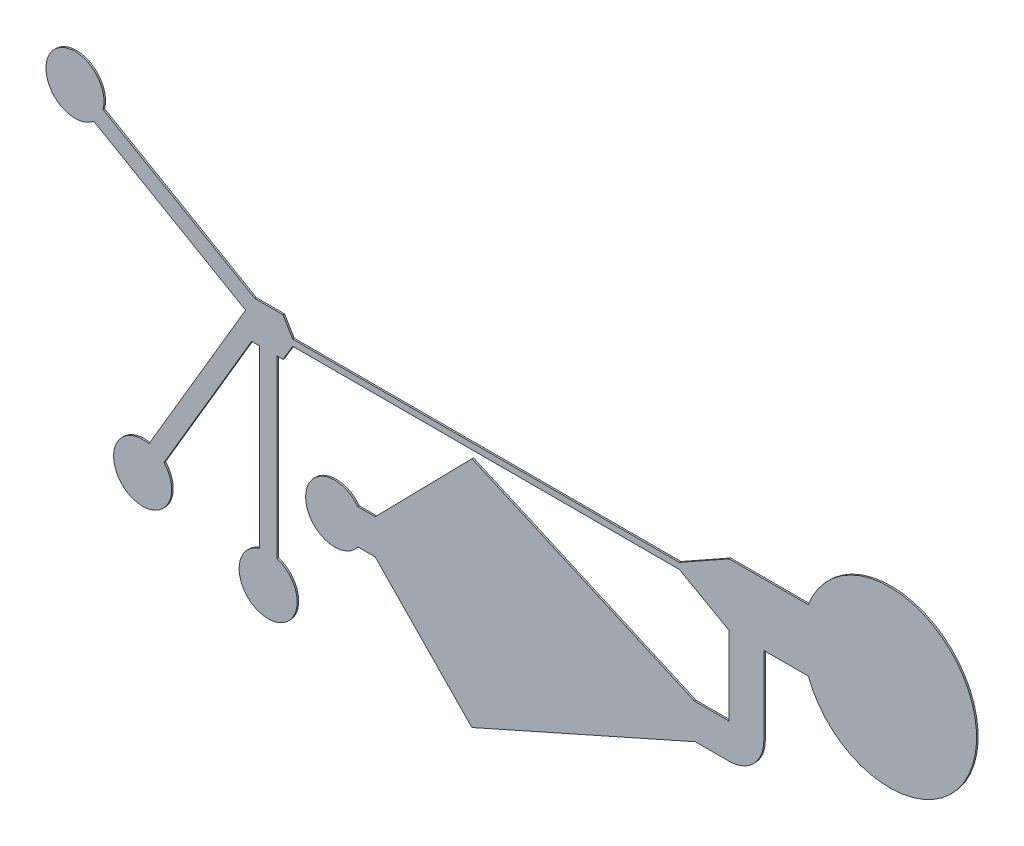
SolidWorks part; units mm, degrees
ref_plane "Front Plane" through (0, 0, 0) normal (0, 0, 1) x (1, 0, 0)
ref_plane "Top Plane" through (0, 0, 0) normal (0, 1, 0) x (1, 0, 0)
ref_plane "Right Plane" through (0, 0, 0) normal (1, 0, 0) x (0, 0, -1)
sketch "Sketch1" plane through (0, 0, 0) normal (0, 0, 1) x (1, 0, 0)
  line L18 (-1.328, 0.6774) -> (-1.078, 0.2574)
  line L19 (-1.078, 0.0974) -> (-1.328, -0.3226)
  line L27 (-1.078, 0.2574) -> (8.922, 0.2574)
  line L28 (-1.078, 0.0974) -> (8.922, 0.0974)
  line L77 (-1.6255, 0.6774) -> (-1.328, 0.6774)
  line L78 (-1.488, -0.3226) -> (-1.328, -0.3226)
  line L79 (-1.488, -0.3226) -> (-1.488, -4.8226)
  line L80 (-1.938, -0.3226) -> (-1.938, -4.8226)
  line L81 (-1.938, -4.8226) -> (-1.938, -4.8572)
  line L82 (-2.138, -0.3226) -> (-4.3759, -4.1198)
  line L83 (-2.138, -0.3226) -> (-1.938, -0.3226)
  line L89 (8.922, 0.2574) -> (10.202, 0.9774)
  line L90 (-4.7636, -3.8914) -> (-2.2957, 0.2962)
  line L91 (-2.2957, 0.2962) -> (-6.1928, 2.5462)
  line L93 (-5.953, 2.9274) -> (-2.4219, 0.8887)
  line L94 (-1.6255, 0.6774) -> (-2.0559, 0.6774)
  line L95 (-4.3759, -4.1198) -> (-4.4053, -4.1697) construction
  line L96 (-1.488, -4.8226) -> (-1.488, -4.8572)
  line L97 (8.922, 0.0974) -> (10.202, -0.6226)
  line L101 (10.202, 0.9774) -> (10.5145, 0.9774)
  line L102 (10.5145, 0.9774) -> (10.9354, 0.9774)
  line L110 (-2.4219, 0.8887) -> (-2.0559, 0.6774)
  line L111 (10.9354, 0.9774) -> (12.252, 0.9774)
  line L113 (-4.7636, -3.8914) -> (-4.795, -3.9447)
  line L114 (-4.3759, -4.1198) -> (-4.4053, -4.1697)
  line L117 (10.202, -0.6226) -> (10.202, -1.4226)
  line L118 (11.102, -0.6226) -> (11.102, -1.4226)
  line L119 (10.202, -1.4226) -> (10.202, -1.5226)
  line L120 (11.102, -1.4226) -> (11.102, -1.5275)
  line L121 (11.102, -1.5275) -> (11.102, -2.3275)
  line L122 (10.202, -1.5226) -> (10.202, -2.3275)
  line L123 (11.102, -0.6226) -> (12.252, -0.6226)
  line L125 (3.5556, 0.0974) -> (3.5556, -0.1026) construction
  line L126 (-1.713, -6.3226) -> (-1.713, -6.4676) construction
  line L127 (-1.713, -6.3226) -> (3.5556, -6.3226) construction
  line L128 (1.054, -2.6535) -> (0.604, -2.6535) construction
  line L129 (-5.953, 2.9274) -> (-5.9824, 2.9454)
  line L134 (-6.1928, 2.5462) -> (-6.2246, 2.5625)
  line L137 (11.102, -2.3275) -> (11.102, -2.6535)
  line L138 (10.202, -2.6535) -> (9.3113, -2.6535)
  line L139 (10.202, -2.6535) -> (10.202, -2.3275)
  line L140 (10.202, -3.5535) -> (9.3317, -3.5535)
  line L141 (3.5556, -0.1026) -> (9.3113, -2.6535)
  line L142 (3.5556, -6.1226) -> (9.3317, -3.5535)
  line L145 (0.604, -2.6535) -> (1.054, -2.6535)
  line L146 (0.6084, -3.5535) -> (1.054, -3.5535)
  line L147 (3.5556, -0.1026) -> (1.054, -2.6535)
  line L148 (1.054, -3.5535) -> (3.5556, -6.1226)
  line L150 (1.054, -3.5535) -> (0.6084, -3.5535) construction
  line L151 (3.5556, -6.1226) -> (3.5556, -6.3226) construction
  arc A10 (-1.938, -4.8572) -> (-1.488, -4.8572) centre (-1.713, -5.5726) ccw
  arc A11 (-4.795, -3.9447) -> (-4.4053, -4.1697) centre (-4.9579, -4.6768) ccw
  arc A15 (12.252, -0.6226) -> (12.252, 0.9774) centre (14.3549, 0.1774) ccw
  arc A17 (-5.9824, 2.9454) -> (-6.2246, 2.5625) centre (-6.7077, 3.1362) ccw
  arc A20 (10.202, -3.5535) -> (11.102, -2.6535) centre (10.202, -2.6535) ccw
  arc A21 (0.604, -2.6535) -> (0.6084, -3.5535) centre (0.0062, -3.1064) ccw
  point P0 (-1.938, -0.3226)
  point P2 (-1.328, 0.6774)
  point P3 (-1.488, -0.3226)
  point P10 (-1.713, -4.8226)
  point P11 (-1.713, -4.8226)
  point P13 (-1.713, -5.5726)
  point P15 (11.102, -0.6226)
  point P20 (-2.138, -0.3226)
  point P23 (-4.5829, -4.0272)
  point P29 (-4.9579, -4.6768)
  point P35 (-1.078, 0.0974)
  point P37 (-1.328, 0.6774)
  point P38 (-1.078, 0.2574)
  point P39 (-1.328, 0.6774)
  point P46 (-6.4316, 2.4239)
  point P48 (-7.0811, 2.7989)
  point P49 (-6.0729, 2.7368)
  point P55 (-1.713, -6.3226)
  point P56 (-6.7077, 3.1362)
  point P60 (1.054, -2.6535)
  point P63 (1.054, -3.5535)
  point P65 (3.5556, -3.1126)
  point P76 (3.5556, -0.1026)
  point P80 (3.5556, 0.0974)
  point P81 (3.5556, -6.1226)
  point P82 (3.5556, -6.3226)
  point P85 (10.202, -2.6535)
  point P86 (10.202, -3.5626)
  point P88 (11.1019, -2.6626)
  dimension "D7" = 0.45
  dimension "D17" = 0.72
  dimension "D23" = 0.8
  dimension "D19" = 1.28
  dimension "D14" = 0.75
  dimension "D31" = 4.5
  dimension "D24" = 0.45
  dimension "D3" = 0.42
  dimension "D4" = 0.42
  dimension "D5" = 1.28
  dimension "D6" = 0.16
  dimension "D8" = 0.25
  dimension "D9" = 0.0345
  dimension "D10" = 0.225
  dimension "D11" = 0.75
  dimension "D12" = 10
  dimension "D13" = 0.2
  dimension "D15" = 0.75
  dimension "D16" = 0.25
  dimension "D18" = 0.72
  dimension "D20" = 0
  dimension "D21" = 0.8
  dimension "D22" = 1.15
  dimension "D25" = 4.5
  dimension "D26" = 0.45
  dimension "D27" = 0.45
  dimension "D28" = 0.16
  dimension "D29" = 0
  dimension "D30" = 10
  dimension "D32" = 0.2
  dimension "D33" = 4.5
  dimension "D34" = 0.2
  dimension "D35" = 0.9
extrude "Boss-Extrude1" add sketch "Sketch1" along normal blind 0.04
